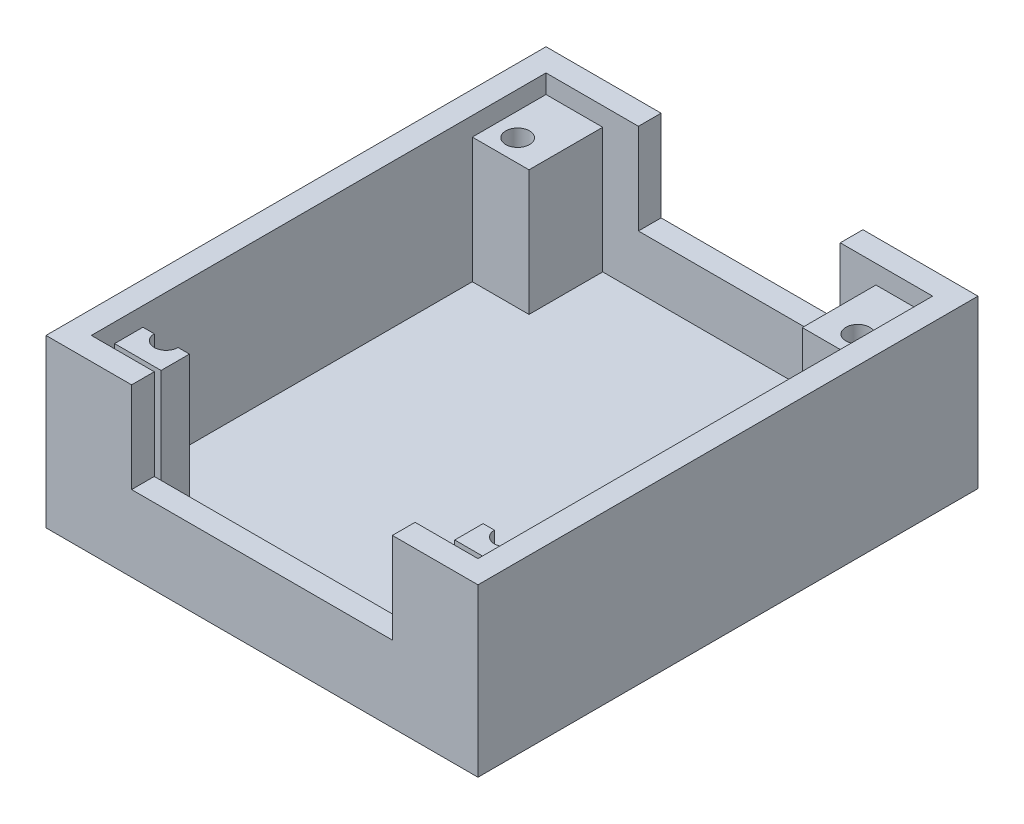
SolidWorks part; units mm, degrees
ref_plane "Front Plane" through (0, 0, 0) normal (0, 0, 1) x (1, 0, 0)
ref_plane "Top Plane" through (0, 0, 0) normal (0, 1, 0) x (1, 0, 0)
ref_plane "Right Plane" through (0, 0, 0) normal (1, 0, 0) x (0, 0, -1)
sketch "Sketch1" plane through (0, 0, 0) normal (0, 1, 0) x (1, 0, 0)
  line L0 (-17.05, 20.05) -> (17.05, -20.05)
  line L1 (-17.05, 20.05) -> (17.05, 20.05)
  line L2 (-17.05, 20.05) -> (-17.05, -20.05)
  line L3 (-17.05, -20.05) -> (17.05, -20.05)
  line L4 (17.05, 20.05) -> (17.05, -20.05)
  dimension "D1" = 34.1
  dimension "D2" = 40.1
extrude "Boss-Extrude1" add sketch "Sketch1" along normal blind 2 contours L2 L3 L0 | L4 L1 L0
sketch "Sketch2" plane through (0, 2, 0) normal (0, 1, 0) x (1, 0, 0)
  line L4 (-19.05, 22.05) -> (-19.05, -22.05)
  line L5 (-19.05, -22.05) -> (19.05, -22.05)
  line L6 (19.05, -22.05) -> (19.05, 22.05)
  line L7 (19.05, 22.05) -> (-19.05, 22.05)
  line L8 (-17.05, 20.05) -> (-17.05, -20.05)
  line L9 (-17.05, -20.05) -> (17.05, -20.05)
  line L10 (17.05, -20.05) -> (17.05, 20.05)
  line L11 (17.05, 20.05) -> (-17.05, 20.05)
  line L12 (-17.05, 20.05) -> (-17.05, -20.05)
  line L13 (-17.05, -20.05) -> (17.05, -20.05)
  line L14 (17.05, -20.05) -> (17.05, 20.05)
  line L15 (17.05, 20.05) -> (-17.05, 20.05)
  dimension "D1" = 0
  dimension "D2" = 2
extrude "Boss-Extrude2" add sketch "Sketch2" along normal blind 12.7 and the other way up to surface (2 mm away) other way up to face at (0, 0, 0)
sketch "Sketch3" plane through (0, 0, 0) normal (0, -1, 0) x (1, 0, 0)
  line L0 (-15, 15.5) -> (15, -15.5) construction
  line L1 (-15, 15.5) -> (15, 15.5) construction
  line L2 (-15, 15.5) -> (-15, -15.5) construction
  line L3 (-15, -15.5) -> (15, -15.5) construction
  line L4 (15, 15.5) -> (15, -15.5) construction
  circle A0 centre (-15, 15.5) radius 1.05
  dimension "D3" = 2.1
  dimension "D1" = 30
  dimension "D2" = 31
sketch "Sketch4" plane through (0, 14.7, 0) normal (0, 1, 0) x (1, 0, 0)
  line L0 (19.05, 22.05) -> (-19.05, 22.05) construction
  line L1 (-8.9, 22.05) -> (8.9, 22.05)
  line L2 (-8.9, 22.05) -> (-8.9, 20.05)
  line L3 (-8.9, 20.05) -> (8.9, 20.05)
  line L4 (8.9, 22.05) -> (8.9, 20.05)
  line L5 (17.05, 20.05) -> (-17.05, 20.05) construction
  line L6 (-17.05, -20.05) -> (17.05, -20.05) construction
  line L7 (-11.5, -20.05) -> (11.5, -20.05)
  line L8 (-11.5, -20.05) -> (-11.5, -22.05)
  line L9 (-11.5, -22.05) -> (11.5, -22.05)
  line L10 (11.5, -20.05) -> (11.5, -22.05)
  line L11 (-19.05, -22.05) -> (19.05, -22.05) construction
  point P8 (0, 20.05)
  point P18 (0, -20.05)
  dimension "D1" = 17.8
  dimension "D2" = 23
extrude "Cut-Extrude1" cut sketch "Sketch4" against normal blind 8
sketch "Sketch5" plane through (0, 2, 0) normal (0, 1, 0) x (1, 0, 0)
  line L0 (-16.05, -15.5) -> (-17.05, -15.5)
  line L1 (-17.05, 20.05) -> (-12.05, 20.05)
  line L2 (-17.05, 20.05) -> (-17.05, 13.55)
  line L3 (-17.05, 13.55) -> (-12.05, 13.55)
  line L4 (-12.05, 20.05) -> (-12.05, 13.55)
  line L5 (17.05, 20.05) -> (12.05, 20.05)
  line L6 (17.05, 20.05) -> (17.05, 13.55)
  line L7 (17.05, 13.55) -> (12.05, 13.55)
  line L8 (12.05, 20.05) -> (12.05, 13.55)
  line L9 (-17.05, 20.05) -> (-17.05, -20.05) construction
  line L10 (-17.05, -15.5) -> (-17.05, -18)
  line L11 (-17.05, -18) -> (-12.95, -18)
  line L13 (-17.05, 20.05) -> (-17.05, -20.05) construction
  line L14 (-12.95, -18) -> (-12.95, -15.5)
  line L15 (-15, -15.5) -> (15, -15.5) construction
  line L16 (-12.95, -15.5) -> (-13.95, -15.5)
  line L17 (0, -8.085) -> (0, 8.085) construction
  line L18 (12.95, -15.5) -> (13.95, -15.5)
  line L19 (12.95, -18) -> (12.95, -15.5)
  line L20 (17.05, -18) -> (12.95, -18)
  line L21 (17.05, -15.5) -> (17.05, -18)
  line L22 (16.05, -15.5) -> (17.05, -15.5)
  circle A0 centre (-15, 15.5) radius 1.05
  circle A1 centre (15, 15.5) radius 1.05
  circle A2 centre (-15, -15.5) radius 1.05 construction
  arc A3 (-16.05, -15.5) -> (-13.95, -15.5) centre (-15, -15.5) ccw
  arc A4 (16.05, -15.5) -> (13.95, -15.5) centre (15, -15.5) cw
  line M22 (-17.05, 20.05) -> (-17.05, -20.05)
  line M24 (17.05, -20.05) -> (17.05, 20.05)
  line M25 (17.05, 20.05) -> (-17.05, 20.05)
  dimension "D5" = 2.1
  dimension "D6" = 2.1
  dimension "D9" = 1.05
  dimension "D1" = 5
  dimension "D2" = 5
  dimension "D3" = 6.5
  dimension "D4" = 6.5
  dimension "D7" = 2.5
  dimension "D8" = 4.1
  dimension "D10" = 1
extrude "Boss-Extrude3" add sketch "Sketch5" along normal offset from surface (11.05 mm away) 1.65 contours A3 L0 L11 L14 L16 M22 | L22 A4 L18 L19 L20 M24 | L8 L7 A1 M25 M24 | L4 L3 A0 M25 M22 up to face at (14.125, 14.7, 0)
extrude "Cut-Extrude2" cut sketch "Sketch3" against normal through all
mirror "Mirror1" about plane through (0, 0, 0) normal (0, 0, 1) of "Cut-Extrude2" second plane through (0, 0, 0) second plane normal (1, 0, 0)
